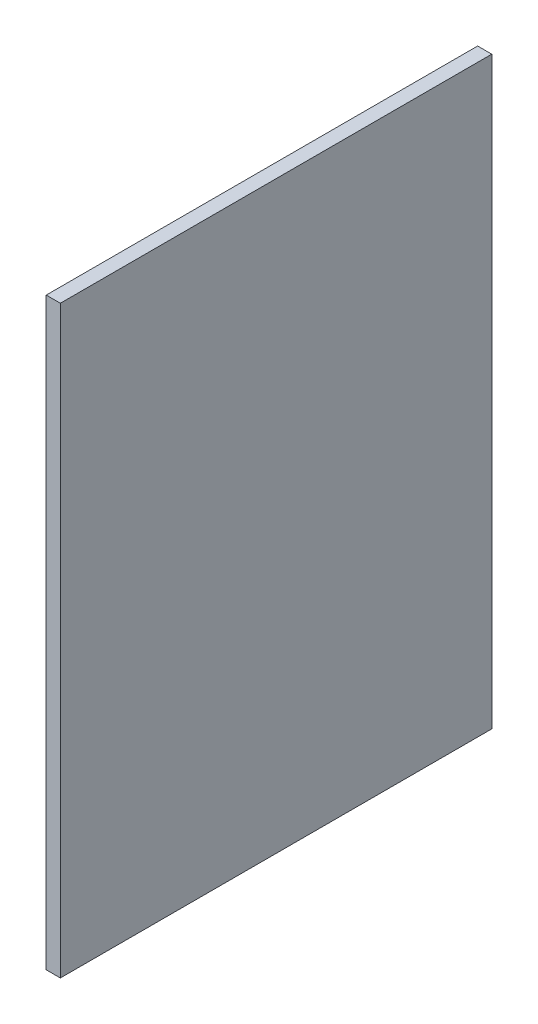
SolidWorks part; units mm, degrees
ref_plane "Front Plane" through (0, 0, 0) normal (0, 0, 1) x (1, 0, 0)
ref_plane "Top Plane" through (0, 0, 0) normal (0, 1, 0) x (1, 0, 0)
ref_plane "Right Plane" through (0, 0, 0) normal (1, 0, 0) x (0, 0, -1)
sketch "Sketch1" plane through (0, 0, 0) normal (1, 0, 0) x (0, 0, -1)
  line L1 (490.2241, -73.8555) -> (-59.7759, -73.8555)
  line L2 (490.2241, -73.8555) -> (490.2241, 671.1445)
  line L3 (490.2241, 671.1445) -> (-59.7759, 671.1445)
  line L4 (-59.7759, -73.8555) -> (-59.7759, 671.1445)
  line L5 (490.2241, -73.8555) -> (-59.7759, 671.1445) construction
  line L6 (490.2241, 671.1445) -> (-59.7759, -73.8555) construction
  point P0 (215.2241, 298.6445)
  dimension "D1" = 745
  dimension "D2" = 550
extrude "Boss-Extrude1" add sketch "Sketch1" along normal blind 18
